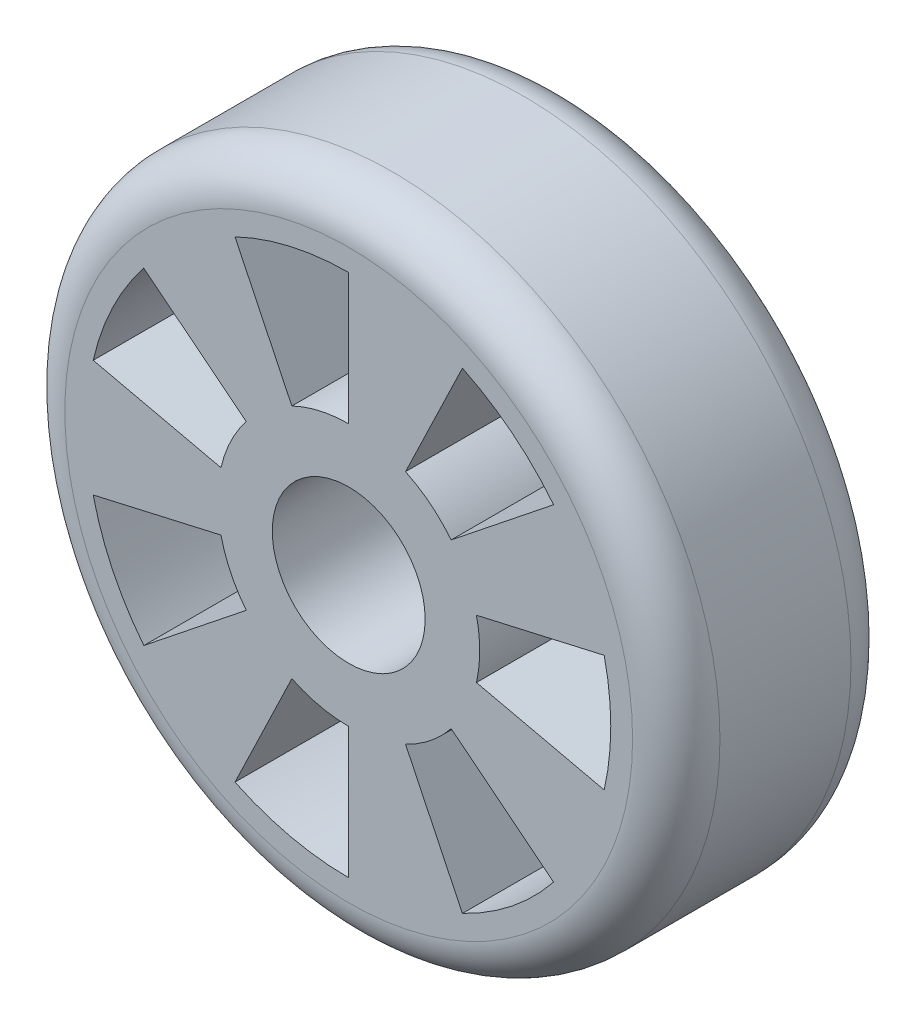
SolidWorks part; units mm, degrees
ref_plane "Front Plane" through (0, 0, 0) normal (0, 0, 1) x (1, 0, 0)
ref_plane "Top Plane" through (0, 0, 0) normal (0, 1, 0) x (1, 0, 0)
ref_plane "Right Plane" through (0, 0, 0) normal (1, 0, 0) x (0, 0, -1)
sketch "Sketch1" plane through (0, 0, 0) normal (0, 0, 1) x (1, 0, 0)
  line L0 (0, 30) -> (0, 60)
  line L1 (13.0165, 27.0291) -> (26.033, 54.0581)
  line L2 (23.4549, 18.7047) -> (46.9099, 37.4094)
  line L3 (29.2478, 6.6756) -> (58.4957, 13.3513)
  line L4 (29.2478, -6.6756) -> (58.4957, -13.3513)
  line L5 (23.4549, -18.7047) -> (46.9099, -37.4094)
  line L6 (13.0165, -27.0291) -> (26.033, -54.0581)
  line L7 (0, -30) -> (0, -60)
  line L8 (-13.0165, -27.0291) -> (-26.033, -54.0581)
  line L9 (-23.4549, -18.7047) -> (-46.9099, -37.4094)
  line L10 (-29.2478, -6.6756) -> (-58.4957, -13.3513)
  line L11 (-29.2478, 6.6756) -> (-58.4957, 13.3513)
  line L12 (-23.4549, 18.7047) -> (-46.9099, 37.4094)
  line L13 (-13.0165, 27.0291) -> (-26.033, 54.0581)
  circle A0 centre (0, 0) radius 75
  arc A2 (-23.4549, 18.7047) -> (-29.2478, 6.6756) centre (0, 0) ccw
  arc A3 (-46.9099, 37.4094) -> (-58.4957, 13.3513) centre (0, 0) ccw
  arc A4 (0, 30) -> (-13.0165, 27.0291) centre (0, 0) ccw
  arc A5 (0, 60) -> (-26.033, 54.0581) centre (0, 0) ccw
  arc A6 (23.4549, 18.7047) -> (13.0165, 27.0291) centre (0, 0) ccw
  arc A7 (46.9099, 37.4094) -> (26.033, 54.0581) centre (0, 0) ccw
  arc A8 (29.2478, -6.6756) -> (29.2478, 6.6756) centre (0, 0) ccw
  arc A9 (58.4957, -13.3513) -> (58.4957, 13.3513) centre (0, 0) ccw
  arc A10 (13.0165, -27.0291) -> (23.4549, -18.7047) centre (0, 0) ccw
  arc A11 (26.033, -54.0581) -> (46.9099, -37.4094) centre (0, 0) ccw
  arc A12 (-13.0165, -27.0291) -> (0, -30) centre (0, 0) ccw
  arc A13 (-26.033, -54.0581) -> (0, -60) centre (0, 0) ccw
  arc A14 (-29.2478, -6.6756) -> (-23.4549, -18.7047) centre (0, 0) ccw
  arc A15 (-58.4957, -13.3513) -> (-46.9099, -37.4094) centre (0, 0) ccw
  point P36 (0, 0)
  dimension "D1" = 150
  dimension "D3" = 60
  dimension "D4" = 120
  dimension "D5" = 14
extrude "Boss-Extrude1" add sketch "Sketch1" against normal blind 50 contours A0
fillet "Fillet1" radius 10 2 edges at (75, 0, 0) (75, 0, -50)
sketch "Sketch4" plane through (0, 0, 0) normal (0, 0, 1) x (1, 0, 0)
  circle A0 centre (0, 0) radius 17.5
  dimension "D1" = 35
extrude "Cut-Extrude1" cut sketch "Sketch4" against normal through all
